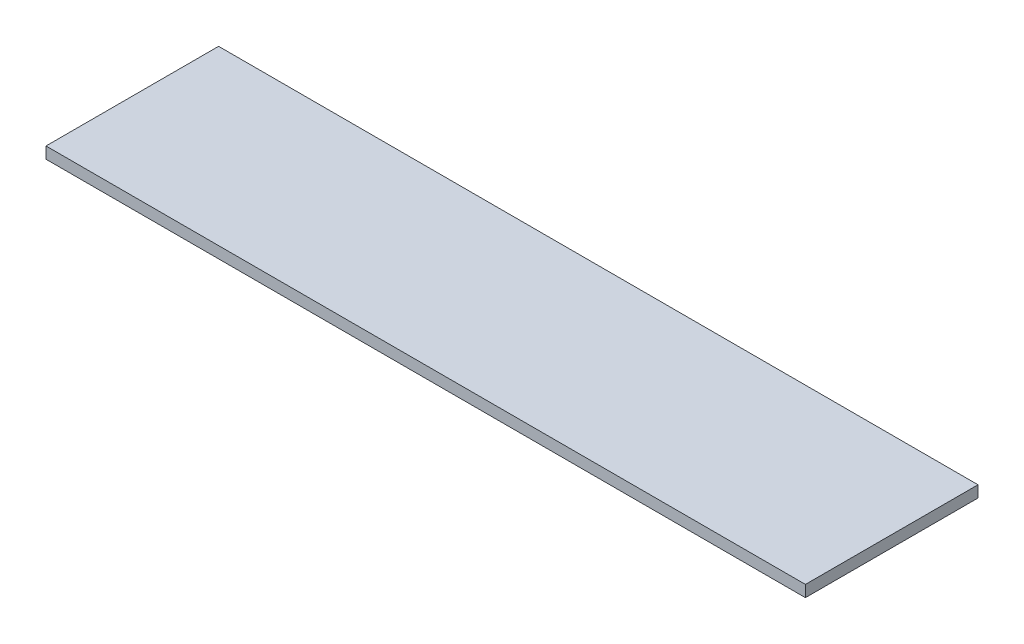
SolidWorks part; units mm, degrees
ref_plane "Front Plane" through (0, 0, 0) normal (0, 0, 1) x (1, 0, 0)
ref_plane "Top Plane" through (0, 0, 0) normal (0, 1, 0) x (1, 0, 0)
ref_plane "Right Plane" through (0, 0, 0) normal (1, 0, 0) x (0, 0, -1)
sketch "Sketch1" plane through (0, 0, 0) normal (0, 1, 0) x (1, 0, 0)
  line L1 (-52.3875, 11.9062) -> (52.3875, 11.9062)
  line L2 (-52.3875, 11.9062) -> (-52.3875, -11.9063)
  line L3 (-52.3875, -11.9063) -> (52.3875, -11.9063)
  line L4 (52.3875, 11.9062) -> (52.3875, -11.9063)
  line L5 (-52.3875, 11.9062) -> (52.3875, -11.9063) construction
  line L6 (-52.3875, -11.9063) -> (52.3875, 11.9062) construction
  point P0 (0, 0)
  dimension "D1" = 104.775
  dimension "D2" = 23.8125
extrude "Boss-Extrude1" add sketch "Sketch1" along normal blind 1.5875
